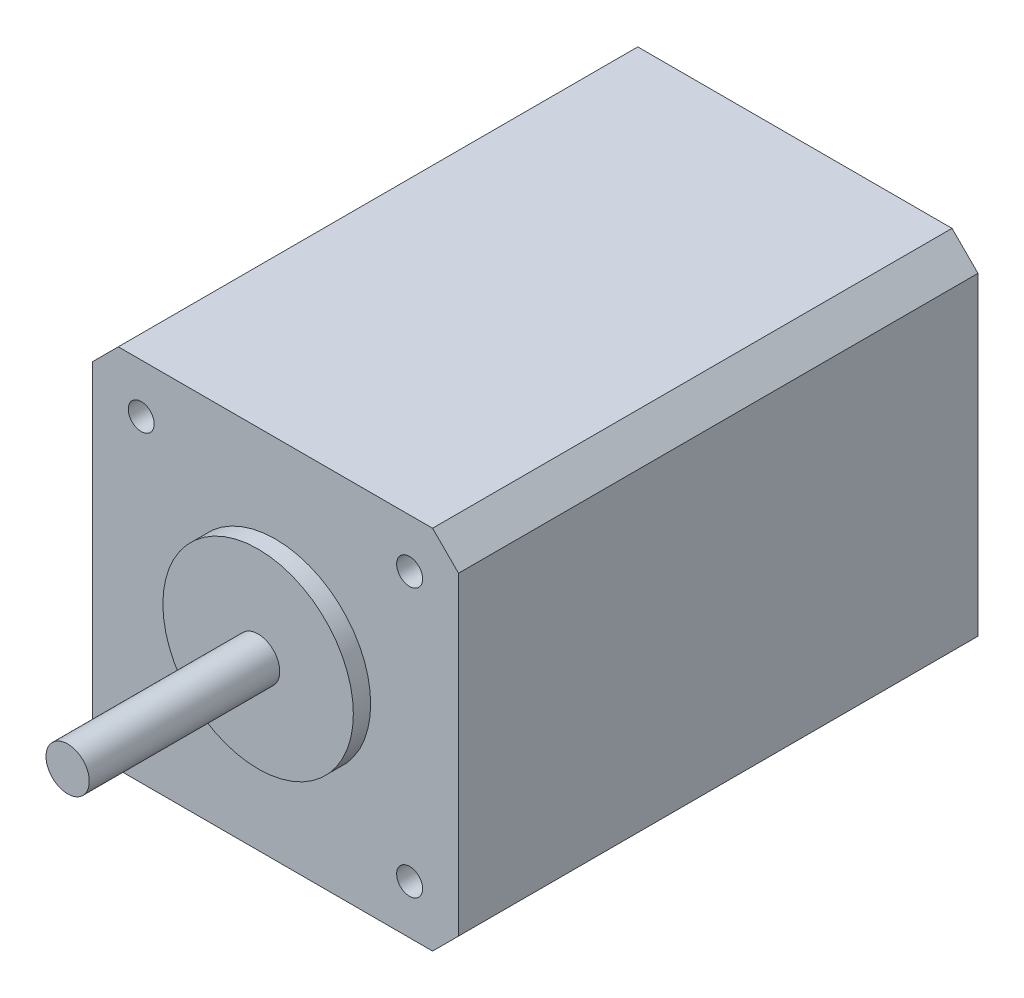
SolidWorks part; units mm, degrees
ref_plane "前视基准面" through (0, 0, 0) normal (0, 0, 1) x (1, 0, 0)
ref_plane "上视基准面" through (0, 0, 0) normal (0, 1, 0) x (1, 0, 0)
ref_plane "右视基准面" through (0, 0, 0) normal (1, 0, 0) x (0, 0, -1)
ref_plane "基准面4" through (0, -21.15, 0) normal (0, -1, 0) x (1, 0, 0)
sketch "草图1" plane through (0, -21.15, 0) normal (0, -1, 0) x (1, 0, 0)
  line L0 (21.15, 55) -> (-21.15, 55)
  line L1 (-21.15, 55) -> (-21.15, -5)
  line L2 (-21.15, -5) -> (21.15, -5)
  line L3 (21.15, -5) -> (21.15, 55)
extrude "凸台-拉伸1" add sketch "草图1" against normal blind 42.3
ref_plane "基准面5" through (0, 0, 0) normal (0, -1, 0) x (1, 0, 0)
sketch "草图2" plane through (0, 0, 0) normal (0, -1, 0) x (1, 0, 0)
  line L0 (2.5, 79) -> (0, 79)
  line L1 (0, 79) -> (0, 55)
  line L2 (0, 55) -> (11, 55)
  line L3 (11, 55) -> (11, 57)
  line L4 (11, 57) -> (2.5, 57)
  line L5 (2.5, 57) -> (2.5, 79)
  line L6 (0, 79) -> (0, 55) construction
revolve "旋转1" add sketch "草图2" angle 360 about L6
hole_wizard "Ø3.0 (3) 直径孔1" positions "草图4" profile "草图3" hole size "Ø3.0" standard "ANSI Metric"
sketch "草图4" plane through (0, 0, 55) normal (0, 0, 1) x (1, 0, 0)
  point P0 (15.5, -15.5)
  point P1 (-15.5, -15.5)
  point P2 (-15.5, 15.5)
  point P3 (15.5, 15.5)
sketch "草图3" plane through (15.5, -15.5, 55) normal (1, 0, 0) x (0, -1, 0)
  line L0 (0, 0) -> (0, 5)
  line L1 (0, 5) -> (1.5, 5)
  line L2 (1.5, 5) -> (1.5, 0)
  line L5 (1.5, 0) -> (0, 0)
  line L10 (0, 5) -> (-1.5, 5) construction
  line L11 (0, -6.35) -> (0, 107.95) construction
  dimension "孔直径" = 3
  dimension "孔深度" = 5
  dimension "导头角度" = 180
chamfer "倒角1" distance 3 angle 45 4 edges at (21.15, 21.15, 25) (-21.15, 21.15, 25) (-21.15, -21.15, 25) (21.15, -21.15, 25)
